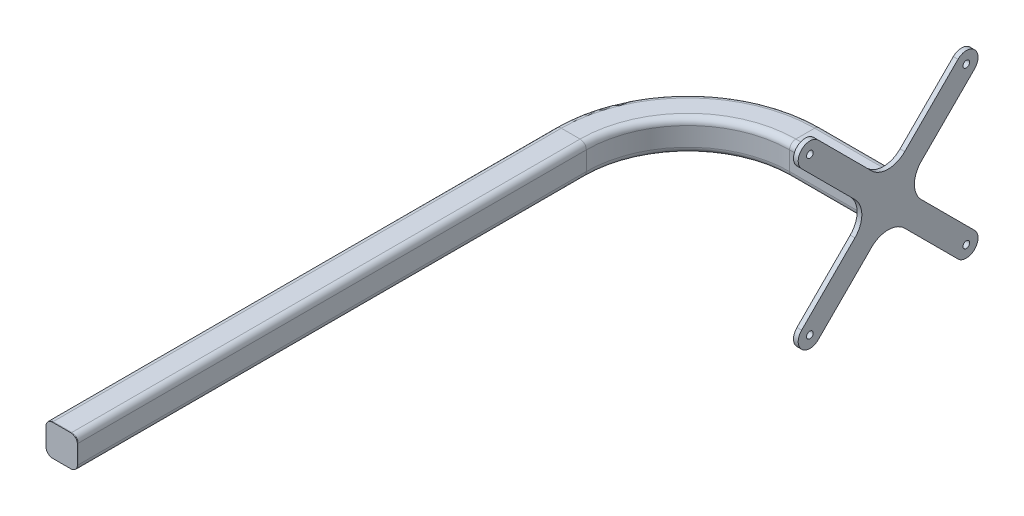
SolidWorks part; units mm, degrees
ref_plane "Front Plane" through (0, 0, 0) normal (0, 0, 1) x (1, 0, 0)
ref_plane "Top Plane" through (0, 0, 0) normal (0, 1, 0) x (1, 0, 0)
ref_plane "Right Plane" through (0, 0, 0) normal (1, 0, 0) x (0, 0, -1)
sketch "Sketch1" plane through (0, 0, 0) normal (0, 1, 0) x (1, 0, 0)
  line L0 (0, 0) -> (0, 650)
  line L1 (150, 800) -> (250, 800)
  arc A0 (0, 650) -> (150, 800) centre (150, 650) cw
  point P6 (0, 800)
  dimension "D2" = 150
  dimension "D1" = 800
  dimension "D3" = 100
other "Square tube 40 X 40 X 4(1)"
ref_plane "Plane1" through (0, 0, 0) normal (0, 0, -1) x (-1, 0, 0)
sketch "Sketch11" plane through (0, 0, 0) normal (0, 0, -1) x (-1, 0, 0)
  line L0 (-12, -16) -> (12, -16)
  line L1 (-16, -12) -> (-16, 12)
  line L2 (12, 16) -> (-12, 16)
  line L3 (16, 12) -> (16, -12)
  line L4 (-12, -20) -> (12, -20)
  line L5 (-20, -12) -> (-20, 12)
  line L6 (12, 20) -> (-12, 20)
  line L7 (20, 12) -> (20, -12)
  arc A0 (20, 12) -> (12, 20) centre (12, 12) ccw
  arc A1 (12, -20) -> (20, -12) centre (12, -12) ccw
  arc A2 (-20, -12) -> (-12, -20) centre (-12, -12) ccw
  arc A3 (-12, 20) -> (-20, 12) centre (-12, 12) ccw
  arc A4 (-12, 16) -> (-16, 12) centre (-12, 12) ccw
  arc A5 (16, 12) -> (12, 16) centre (12, 12) ccw
  arc A6 (12, -16) -> (16, -12) centre (12, -12) ccw
  arc A7 (-16, -12) -> (-12, -16) centre (-12, -12) ccw
  point P0 (-20, 0)
  point P1 (20, 0)
  point P2 (0, 20)
  point P3 (0, -20)
  point P4 (0, 0)
  point P5 (-20, -20)
  point P6 (20, -20)
  point P7 (20, 20)
  point P8 (-20, 20)
  point P33 (0, 0)
  dimension "D1" = 8
  dimension "Thickness" = 4
  dimension "V_leg" = 40
sketch "Sketch12" plane through (0, 0, 0) normal (0, 0, 1) x (1, 0, 0)
  line L0 (150, 20) -> (12, 20) construction
  line L1 (-11.581, -20) -> (11.581, -20)
  line L2 (-20.081, -11.5) -> (-20.081, 11.5)
  line L3 (-11.581, 20) -> (11.581, 20)
  line L4 (20.081, -11.5) -> (20.081, 11.5)
  line L5 (-20.081, -20) -> (20.081, 20) construction
  line L6 (-20.081, 20) -> (20.081, -20) construction
  arc A0 (11.581, 20) -> (20.081, 11.5) centre (11.581, 11.5) cw
  arc A1 (11.581, -20) -> (20.081, -11.5) centre (11.581, -11.5) ccw
  arc A2 (-11.581, -20) -> (-20.081, -11.5) centre (-11.581, -11.5) cw
  arc A3 (-20.081, 11.5) -> (-11.581, 20) centre (-11.581, 11.5) cw
  point P0 (0, 0)
  dimension "D1" = 8.5
extrude "Boss-Extrude1" add sketch "Sketch12" along normal blind 1 separate body
sketch "Sketch13" plane through (250, 0, 0) normal (1, 0, 0) x (0, 0, -1)
  line L0 (842.4264, 21.2132) -> (910.6066, 89.3934)
  line L13 (821.2132, -42.4264) -> (889.3934, -110.6066)
  line L14 (778.7868, -42.4264) -> (710.6066, -110.6066)
  line L15 (757.5736, -21.2132) -> (689.3934, -89.3934)
  line L16 (757.5736, 21.2132) -> (689.3934, 89.3934)
  line L17 (842.4264, -21.2132) -> (910.6066, -89.3934)
  line L18 (778.7868, 42.4264) -> (710.6066, 110.6066)
  line L19 (821.2132, 42.4264) -> (889.3934, 110.6066)
  arc A0 (842.4264, 21.2132) -> (842.4264, -21.2132) centre (863.6396, 0) ccw
  arc A1 (821.2132, -42.4264) -> (778.7868, -42.4264) centre (800, -63.6396) ccw
  arc A2 (757.5736, -21.2132) -> (757.5736, 21.2132) centre (736.3604, 0) ccw
  arc A3 (778.7868, 42.4264) -> (821.2132, 42.4264) centre (800, 63.6396) ccw
  arc A4 (910.6066, 89.3934) -> (889.3934, 110.6066) centre (900, 100) ccw
  arc A5 (889.3934, -110.6066) -> (910.6066, -89.3934) centre (900, -100) ccw
  arc A6 (689.3934, -89.3934) -> (710.6066, -110.6066) centre (700, -100) ccw
  arc A7 (710.6066, 110.6066) -> (689.3934, 89.3934) centre (700, 100) ccw
  circle A8 centre (900, 100) radius 4.25
  circle A9 centre (900, -100) radius 4.25
  circle A10 centre (700, -100) radius 4.25
  circle A11 centre (700, 100) radius 4.25
  point P0 (800, 0)
  point P28 (800, 0)
  point P37 (800, 0)
  point P38 (800, 0)
  dimension "D7" = 30
  dimension "D2" = 4
  dimension "D1" = 4
  dimension "D3" = 4
extrude "Boss-Extrude2" add sketch "Sketch13" along normal blind 6 separate body
